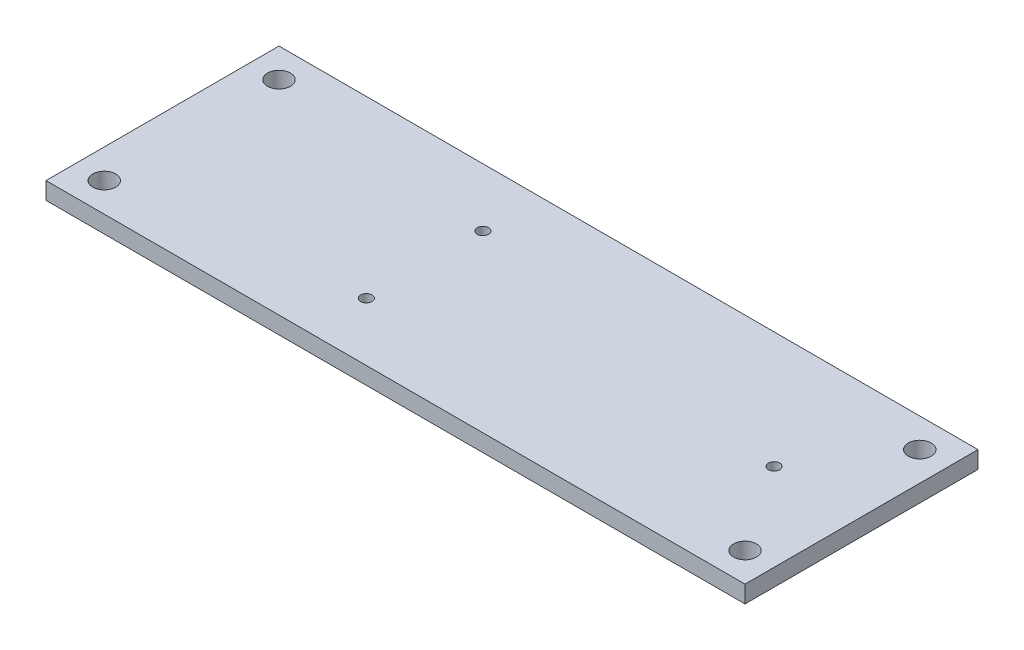
SolidWorks part; units mm, degrees
ref_plane "Front Plane" through (0, 0, 0) normal (0, 0, 1) x (1, 0, 0)
ref_plane "Top Plane" through (0, 0, 0) normal (0, 1, 0) x (1, 0, 0)
ref_plane "Right Plane" through (0, 0, 0) normal (1, 0, 0) x (0, 0, -1)
sketch "Sketch1" plane through (0, 0, 0) normal (0, 1, 0) x (1, 0, 0)
  line L0 (0, 10.16) -> (60.96, 10.16) construction
  line L1 (0, 0) -> (60.96, 0)
  line L2 (0, 0) -> (0, 20.32)
  line L3 (0, 20.32) -> (60.96, 20.32)
  line L4 (60.96, 0) -> (60.96, 20.32)
  line L5 (30.48, 0) -> (30.48, 20.32) construction
  line L7 (58.42, 17.78) -> (58.42, 2.54) construction
  circle A0 centre (2.54, 2.54) radius 1
  circle A1 centre (58.42, 2.54) radius 1
  circle A2 centre (58.42, 17.78) radius 1
  circle A3 centre (2.54, 17.78) radius 1
  circle A4 centre (22.86, 5.08) radius 0.5
  circle A5 centre (53.34, 10.16) radius 0.5
  circle A6 centre (22.86, 15.24) radius 0.5
  dimension "D3" = 2
  dimension "D6" = 1
  dimension "D8" = 7.62
  dimension "D1" = 60.96
  dimension "D2" = 20.32
  dimension "D4" = 2.54
  dimension "D5" = 2.54
  dimension "D7" = 22.86
  dimension "D9" = 5.08
extrude "Boss-Extrude1" add sketch "Sketch1" along normal blind 1.5
